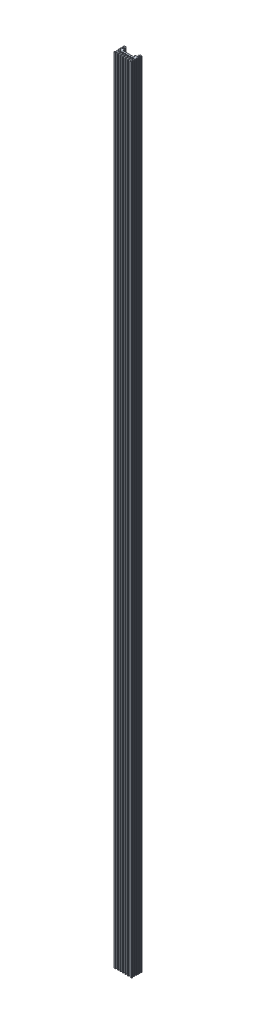
SolidWorks part; units mm, degrees
ref_plane "Alzado" through (0, 0, 0) normal (0, 0, 1) x (1, 0, 0)
ref_plane "Planta" through (0, 0, 0) normal (0, 1, 0) x (1, 0, 0)
ref_plane "Vista lateral" through (0, 0, 0) normal (1, 0, 0) x (0, 0, -1)
sketch "Croquis1" plane through (0, 0, 0) normal (0, 1, 0) x (1, 0, 0)
  line L0 (-12.7958, 0) -> (-12.3447, 0)
  line L1 (-14.9703, 0.3) -> (-14.9703, 4.7055)
  line L2 (-14.7158, 4.96) -> (-13.3047, 4.96)
  line L3 (-13.0503, 4.7055) -> (-13.0503, 0.2545)
  line L4 (-12.0903, 0.2545) -> (-12.0903, 4.7055)
  line L5 (-11.8358, 4.96) -> (-10.4247, 4.96)
  line L6 (-16.7958, 0) -> (-15.2703, 0)
  line L7 (-10.1703, 4.7055) -> (-10.1703, 0.2545)
  line L8 (-9.9158, 0) -> (-9.4647, 0)
  line L9 (-9.2103, 0.2545) -> (-9.2103, 4.7055)
  line L10 (-8.9558, 4.96) -> (-7.5447, 4.96)
  line L11 (-7.2903, 4.7055) -> (-7.2903, 0.2545)
  line L12 (-14.3303, 10.9866) -> (-14.3303, 9.9046)
  line L13 (-17.0503, 0.2545) -> (-17.0503, 0.7055)
  line L14 (-16.7958, 0.96) -> (-16.3447, 0.96)
  line L15 (-16.0903, 1.2145) -> (-16.0903, 2.3055)
  line L16 (-16.3447, 2.56) -> (-16.7958, 2.56)
  line L17 (-17.0503, 2.8145) -> (-17.0503, 3.2655)
  line L18 (-16.7958, 3.52) -> (-16.3447, 3.52)
  line L19 (-16.0903, 3.7745) -> (-16.0903, 4.7055)
  line L20 (-16.0903, 4.96) -> (-16.0903, 5.92) construction
  line L21 (-17.0503, 7.2015) -> (-17.0503, 7.9)
  line L22 (-16.8703, 8.08) -> (-15.6323, 8.08)
  line L23 (-16.3447, 4.96) -> (-16.7958, 4.96)
  line L24 (-17.0503, 5.2145) -> (-17.0503, 5.7995)
  line L25 (-15.4523, 8.26) -> (-15.4523, 8.66)
  line L26 (-15.6323, 8.84) -> (-16.8703, 8.84)
  line L27 (-17.0503, 9.02) -> (-17.0503, 9.62)
  line L28 (-16.8703, 9.8) -> (-15.6323, 9.8)
  line L29 (-15.4523, 9.98) -> (-15.4523, 10.58)
  line L30 (-15.6323, 10.76) -> (-16.8703, 10.76)
  line L31 (-17.0503, 10.94) -> (-17.0503, 11.5822)
  line L32 (-7.0358, 0) -> (-6.5847, 0)
  line L33 (2.4697, 4.96) -> (2.4697, 5.92) construction
  line L34 (-12.3739, 7.72) -> (-12.9379, 7.72)
  line L35 (-14.2983, 8.68) -> (-12.3739, 8.68)
  line L36 (0.6777, 8.68) -> (-1.2466, 8.68)
  line L37 (-12.9379, 6.4) -> (-0.6826, 6.4)
  line L38 (-1.2466, 7.72) -> (-0.6826, 7.72)
  line L39 (3.4297, 10.94) -> (3.4297, 11.5822)
  line L40 (2.0117, 10.76) -> (3.2497, 10.76)
  line L41 (1.8317, 9.98) -> (1.8317, 10.58)
  line L42 (3.2497, 9.8) -> (2.0117, 9.8)
  line L43 (3.4297, 9.02) -> (3.4297, 9.62)
  line L44 (2.0117, 8.84) -> (3.2497, 8.84)
  line L45 (1.8317, 8.26) -> (1.8317, 8.66)
  line L46 (3.4297, 5.2145) -> (3.4297, 5.7995)
  line L47 (2.7242, 4.96) -> (3.1753, 4.96)
  line L48 (3.2497, 8.08) -> (2.0117, 8.08)
  line L49 (3.4297, 7.2015) -> (3.4297, 7.9)
  line L50 (2.4697, 3.7745) -> (2.4697, 4.7055)
  line L51 (3.1753, 3.52) -> (2.7242, 3.52)
  line L52 (3.4297, 2.8145) -> (3.4297, 3.2655)
  line L53 (2.7242, 2.56) -> (3.1753, 2.56)
  line L54 (2.4697, 1.2145) -> (2.4697, 2.3055)
  line L55 (3.1753, 0.96) -> (2.7242, 0.96)
  line L56 (3.4297, 0.2545) -> (3.4297, 0.7055)
  line L57 (0.7097, 10.9866) -> (0.7097, 9.9046)
  line L58 (-6.3303, 4.7055) -> (-6.3303, 0.2545)
  line L59 (-4.6647, 4.96) -> (-6.0758, 4.96)
  line L60 (-4.4103, 0.2545) -> (-4.4103, 4.7055)
  line L61 (-3.7047, 0) -> (-4.1558, 0)
  line L62 (-3.4503, 4.7055) -> (-3.4503, 0.2545)
  line L63 (3.1753, 0) -> (1.6497, 0)
  line L64 (-1.7847, 4.96) -> (-3.1958, 4.96)
  line L65 (-1.5303, 0.2545) -> (-1.5303, 4.7055)
  line L66 (-0.5703, 4.7055) -> (-0.5703, 0.2545)
  line L67 (1.0953, 4.96) -> (-0.3158, 4.96)
  line L68 (1.3497, 0.3) -> (1.3497, 4.7055)
  line L69 (-0.8247, 0) -> (-1.2758, 0)
  line L70 (-16.0903, 6.52) -> (-16.033, 0) construction
  arc A0 (-15.2703, 0) -> (-14.9703, 0.3) centre (-15.2703, 0.3) ccw
  arc A1 (-16.0903, 5.92) -> (-16.0903, 7.12) centre (-16.0903, 6.52) ccw
  arc A2 (-16.0903, 3.7745) -> (-16.3447, 3.52) centre (-16.3447, 3.7745) cw
  arc A3 (-16.3447, 0.96) -> (-16.0903, 1.2145) centre (-16.3447, 1.2145) ccw
  arc A4 (-16.0903, 2.3055) -> (-16.3447, 2.56) centre (-16.3447, 2.3055) ccw
  arc A5 (-7.2903, 4.7055) -> (-7.5447, 4.96) centre (-7.5447, 4.7055) ccw
  arc A6 (-9.2103, 4.7055) -> (-8.9558, 4.96) centre (-8.9558, 4.7055) cw
  arc A7 (-10.1703, 4.7055) -> (-10.4247, 4.96) centre (-10.4247, 4.7055) ccw
  arc A8 (-12.0903, 4.7055) -> (-11.8358, 4.96) centre (-11.8358, 4.7055) cw
  arc A9 (-13.3047, 4.96) -> (-13.0503, 4.7055) centre (-13.3047, 4.7055) cw
  arc A10 (-14.7158, 4.96) -> (-14.9703, 4.7055) centre (-14.7158, 4.7055) ccw
  arc A11 (-7.0358, 0) -> (-7.2903, 0.2545) centre (-7.0358, 0.2545) cw
  arc A12 (-9.4647, 0) -> (-9.2103, 0.2545) centre (-9.4647, 0.2545) ccw
  arc A13 (-9.9158, 0) -> (-10.1703, 0.2545) centre (-9.9158, 0.2545) cw
  arc A14 (-12.3447, 0) -> (-12.0903, 0.2545) centre (-12.3447, 0.2545) ccw
  arc A15 (-12.7958, 0) -> (-13.0503, 0.2545) centre (-12.7958, 0.2545) cw
  arc A16 (-17.0503, 0.7055) -> (-16.7958, 0.96) centre (-16.7958, 0.7055) cw
  arc A17 (-17.0503, 0.2545) -> (-16.7958, 0) centre (-16.7958, 0.2545) ccw
  arc A18 (-17.0503, 2.8145) -> (-16.7958, 2.56) centre (-16.7958, 2.8145) ccw
  arc A19 (-17.0503, 3.2655) -> (-16.7958, 3.52) centre (-16.7958, 3.2655) cw
  arc A20 (-16.9311, 6.015) -> (-16.0903, 5.92) centre (-16.5703, 5.44) cw
  arc A21 (-16.9785, 7.0577) -> (-16.0903, 7.12) centre (-16.5703, 7.6) ccw
  arc A22 (-16.9311, 6.015) -> (-17.0503, 5.7995) centre (-16.7958, 5.7995) ccw
  arc A23 (-16.0903, 4.7055) -> (-16.3447, 4.96) centre (-16.3447, 4.7055) ccw
  arc A24 (-16.7958, 4.96) -> (-17.0503, 5.2145) centre (-16.7958, 5.2145) cw
  arc A25 (-14.5452, 9.6532) -> (-14.3555, 8.6735) centre (-14.4677, 9.16) ccw
  arc A26 (-14.5483, 11.2385) -> (-15.1303, 12.1913) centre (-14.4443, 11.9561) cw
  arc A27 (-14.3555, 8.6735) -> (-14.2983, 8.68) centre (-14.2983, 8.4255) cw
  arc A28 (-14.3303, 9.9046) -> (-14.5452, 9.6532) centre (-14.5847, 9.9046) cw
  arc A29 (-14.5483, 11.2385) -> (-14.3303, 10.9866) centre (-14.5847, 10.9866) cw
  arc A30 (-12.1584, 8.5608) -> (-12.1584, 7.8392) centre (-12.7334, 8.2) cw
  arc A31 (-13.142, 7.6175) -> (-13.142, 6.5025) centre (-12.3934, 7.06) ccw
  arc A32 (-13.142, 6.5025) -> (-12.9379, 6.4) centre (-12.9379, 6.6545) ccw
  arc A33 (-12.9379, 7.72) -> (-13.142, 7.6175) centre (-12.9379, 7.4655) ccw
  arc A34 (-12.1584, 7.8392) -> (-12.3739, 7.72) centre (-12.3739, 7.9745) cw
  arc A35 (-12.1584, 8.5608) -> (-12.3739, 8.68) centre (-12.3739, 8.4255) ccw
  arc A36 (-17.0503, 11.5822) -> (-16.917, 11.7561) centre (-16.8703, 11.5822) cw
  arc A37 (-16.8703, 10.76) -> (-17.0503, 10.94) centre (-16.8703, 10.94) cw
  arc A38 (-15.4523, 10.58) -> (-15.6323, 10.76) centre (-15.6323, 10.58) ccw
  arc A39 (-15.6323, 9.8) -> (-15.4523, 9.98) centre (-15.6323, 9.98) ccw
  arc A40 (-17.0503, 7.2015) -> (-16.9785, 7.0577) centre (-16.8703, 7.2015) ccw
  arc A41 (-17.0503, 7.9) -> (-16.8703, 8.08) centre (-16.8703, 7.9) cw
  arc A42 (-17.0503, 9.62) -> (-16.8703, 9.8) centre (-16.8703, 9.62) cw
  arc A43 (-16.8703, 8.84) -> (-17.0503, 9.02) centre (-16.8703, 9.02) cw
  arc A44 (-15.6323, 8.08) -> (-15.4523, 8.26) centre (-15.6323, 8.26) ccw
  arc A45 (-15.4523, 8.66) -> (-15.6323, 8.84) centre (-15.6323, 8.66) ccw
  arc A46 (3.2964, 11.7561) -> (1.5097, 12.1913) centre (-6.8103, -25.85) ccw
  arc A47 (1.8317, 8.66) -> (2.0117, 8.84) centre (2.0117, 8.66) cw
  arc A48 (2.0117, 8.08) -> (1.8317, 8.26) centre (2.0117, 8.26) cw
  arc A49 (3.2497, 8.84) -> (3.4297, 9.02) centre (3.2497, 9.02) ccw
  arc A50 (-16.917, 11.7561) -> (-15.1303, 12.1913) centre (-6.8103, -25.85) cw
  arc A51 (3.4297, 9.62) -> (3.2497, 9.8) centre (3.2497, 9.62) ccw
  arc A52 (3.4297, 7.9) -> (3.2497, 8.08) centre (3.2497, 7.9) ccw
  arc A53 (3.4297, 7.2015) -> (3.358, 7.0577) centre (3.2497, 7.2015) cw
  arc A54 (2.0117, 9.8) -> (1.8317, 9.98) centre (2.0117, 9.98) cw
  arc A55 (1.8317, 10.58) -> (2.0117, 10.76) centre (2.0117, 10.58) cw
  arc A56 (3.2497, 10.76) -> (3.4297, 10.94) centre (3.2497, 10.94) ccw
  arc A57 (3.4297, 11.5822) -> (3.2964, 11.7561) centre (3.2497, 11.5822) ccw
  arc A58 (-1.4621, 8.5608) -> (-1.2466, 8.68) centre (-1.2466, 8.4255) cw
  arc A59 (-1.4621, 7.8392) -> (-1.2466, 7.72) centre (-1.2466, 7.9745) ccw
  arc A60 (-0.6826, 7.72) -> (-0.4786, 7.6175) centre (-0.6826, 7.4655) cw
  arc A61 (-0.4786, 6.5025) -> (-0.6826, 6.4) centre (-0.6826, 6.6545) cw
  arc A62 (-0.4786, 7.6175) -> (-0.4786, 6.5025) centre (-1.2271, 7.06) cw
  arc A63 (-1.4621, 8.5608) -> (-1.4621, 7.8392) centre (-0.8871, 8.2) ccw
  arc A64 (0.9277, 11.2385) -> (0.7097, 10.9866) centre (0.9642, 10.9866) ccw
  arc A65 (0.7097, 9.9046) -> (0.9247, 9.6532) centre (0.9642, 9.9046) ccw
  arc A66 (0.7349, 8.6735) -> (0.6777, 8.68) centre (0.6777, 8.4255) ccw
  arc A67 (0.9277, 11.2385) -> (1.5097, 12.1913) centre (0.8238, 11.9561) ccw
  arc A68 (0.9247, 9.6532) -> (0.7349, 8.6735) centre (0.8472, 9.16) cw
  arc A69 (3.1753, 4.96) -> (3.4297, 5.2145) centre (3.1753, 5.2145) ccw
  arc A70 (2.4697, 4.7055) -> (2.7242, 4.96) centre (2.7242, 4.7055) cw
  arc A71 (3.3105, 6.015) -> (3.4297, 5.7995) centre (3.1753, 5.7995) cw
  arc A72 (3.358, 7.0577) -> (2.4697, 7.12) centre (2.9497, 7.6) cw
  arc A73 (3.3105, 6.015) -> (2.4697, 5.92) centre (2.9497, 5.44) ccw
  arc A74 (3.4297, 3.2655) -> (3.1753, 3.52) centre (3.1753, 3.2655) ccw
  arc A75 (3.4297, 2.8145) -> (3.1753, 2.56) centre (3.1753, 2.8145) cw
  arc A76 (3.4297, 0.2545) -> (3.1753, 0) centre (3.1753, 0.2545) cw
  arc A77 (3.4297, 0.7055) -> (3.1753, 0.96) centre (3.1753, 0.7055) ccw
  arc A78 (-0.8247, 0) -> (-0.5703, 0.2545) centre (-0.8247, 0.2545) ccw
  arc A79 (-1.2758, 0) -> (-1.5303, 0.2545) centre (-1.2758, 0.2545) cw
  arc A80 (-3.7047, 0) -> (-3.4503, 0.2545) centre (-3.7047, 0.2545) ccw
  arc A81 (-4.1558, 0) -> (-4.4103, 0.2545) centre (-4.1558, 0.2545) cw
  arc A82 (-6.5847, 0) -> (-6.3303, 0.2545) centre (-6.5847, 0.2545) ccw
  arc A83 (1.0953, 4.96) -> (1.3497, 4.7055) centre (1.0953, 4.7055) cw
  arc A84 (-0.3158, 4.96) -> (-0.5703, 4.7055) centre (-0.3158, 4.7055) ccw
  arc A85 (-1.5303, 4.7055) -> (-1.7847, 4.96) centre (-1.7847, 4.7055) ccw
  arc A86 (-3.4503, 4.7055) -> (-3.1958, 4.96) centre (-3.1958, 4.7055) cw
  arc A87 (-4.4103, 4.7055) -> (-4.6647, 4.96) centre (-4.6647, 4.7055) ccw
  arc A88 (-6.3303, 4.7055) -> (-6.0758, 4.96) centre (-6.0758, 4.7055) cw
  arc A89 (2.4697, 2.3055) -> (2.7242, 2.56) centre (2.7242, 2.3055) cw
  arc A90 (2.7242, 0.96) -> (2.4697, 1.2145) centre (2.7242, 1.2145) cw
  arc A91 (2.4697, 3.7745) -> (2.7242, 3.52) centre (2.7242, 3.7745) ccw
  arc A92 (2.4697, 5.92) -> (2.4697, 7.12) centre (2.4697, 6.52) cw
  arc A93 (1.6497, 0) -> (1.3497, 0.3) centre (1.6497, 0.3) cw
  point P105 (3.4297, 11.72)
  point P116 (-17.0503, 11.72)
  point P262 (-6.8103, 6.4)
  dimension "D1" = 0.3
  dimension "D2" = 0.2545
  dimension "D3" = 0.2545
  dimension "D4" = 0.2545
  dimension "D6" = 0.2545
  dimension "D7" = 0.18
extrude "Saliente-Extruir1" add sketch "Croquis1" along normal blind 920
